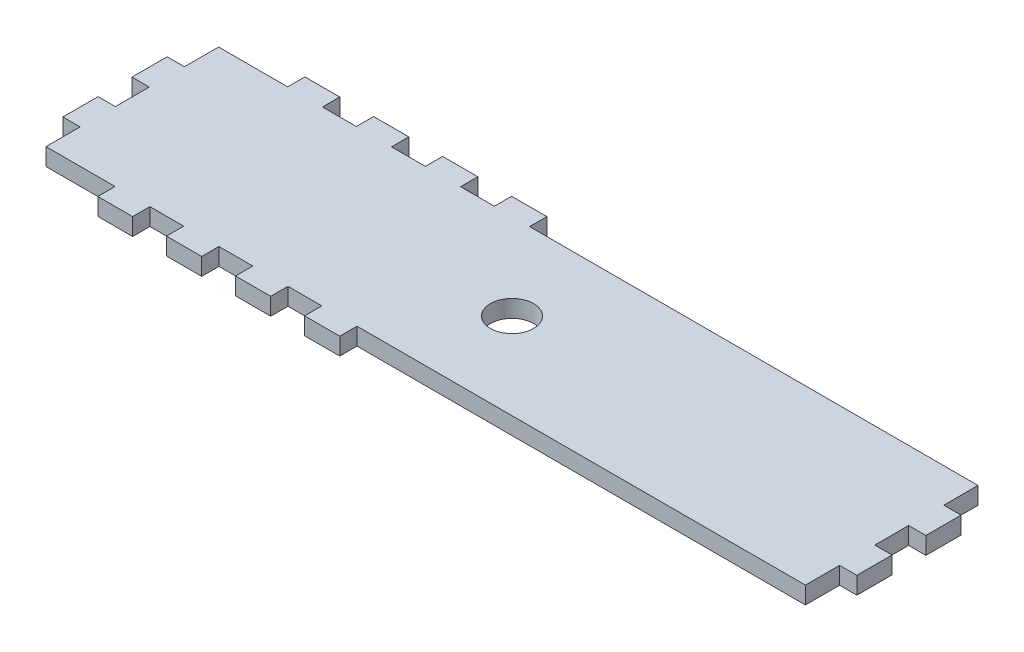
SolidWorks part; units mm, degrees
material "Maple"
ref_plane "Front Plane" through (0, 0, 0) normal (0, 0, 1) x (1, 0, 0)
ref_plane "Top Plane" through (0, 0, 0) normal (0, 1, 0) x (1, 0, 0)
ref_plane "Right Plane" through (0, 0, 0) normal (1, 0, 0) x (0, 0, -1)
sketch "Sketch1" plane through (0, 0, 0) normal (0, 1, 0) x (1, 0, 0)
  line L0 (0, 0) -> (279.4, 0) construction
  line L1 (279.4, 0) -> (279.4, -12.573)
  line L2 (279.4, -12.573) -> (285.75, -12.573)
  line L3 (285.75, -12.573) -> (285.75, -25.527)
  line L4 (285.75, -25.527) -> (279.4, -25.527)
  line L5 (279.4, -25.527) -> (279.4, -37.973)
  line L6 (279.4, -37.973) -> (285.75, -37.973)
  line L7 (285.75, -37.973) -> (285.75, -50.927)
  line L8 (285.75, -50.927) -> (279.4, -50.927)
  line L9 (279.4, -50.927) -> (279.4, -63.5)
  line L10 (279.4, -63.5) -> (0, -63.5) construction
  line L11 (0, -63.5) -> (0, -50.927)
  line L12 (0, -50.927) -> (-6.35, -50.927)
  line L13 (-6.35, -50.927) -> (-6.35, -37.973)
  line L14 (-6.35, -37.973) -> (0, -37.973)
  line L15 (0, -37.973) -> (0, -25.527)
  line L16 (0, -25.527) -> (-6.35, -25.527)
  line L17 (-6.35, -25.527) -> (-6.35, -12.573)
  line L18 (-6.35, -12.573) -> (0, -12.573)
  line L19 (0, -12.573) -> (0, 0)
  line L20 (25.4, 0) -> (25.4, 6.35)
  line L21 (25.4, 6.35) -> (38.227, 6.35)
  line L22 (38.227, 6.35) -> (38.227, 0)
  line L23 (50.673, 0) -> (50.673, 6.35)
  line L24 (50.673, 6.35) -> (63.627, 6.35)
  line L25 (63.627, 6.35) -> (63.627, 0)
  line L26 (76.073, 0) -> (76.073, 6.35)
  line L27 (76.073, 6.35) -> (89.027, 6.35)
  line L28 (89.027, 6.35) -> (89.027, 0)
  line L29 (101.473, 0) -> (101.473, 6.35)
  line L30 (101.473, 6.35) -> (114.427, 6.35)
  line L31 (114.427, 6.35) -> (114.427, 0)
  line L32 (279.4, 0) -> (114.427, 0)
  line L33 (101.473, 0) -> (89.027, 0)
  line L34 (76.073, 0) -> (63.627, 0)
  line L35 (50.673, 0) -> (38.227, 0)
  line L36 (25.4, 0) -> (0, 0)
  line L37 (279.4, -31.75) -> (0, -31.75) construction
  line L38 (0, -63.5) -> (279.4, -63.5) construction
  line L39 (25.4, -63.5) -> (0, -63.5)
  line L40 (50.673, -63.5) -> (38.227, -63.5)
  line L41 (76.073, -63.5) -> (63.627, -63.5)
  line L42 (101.473, -63.5) -> (89.027, -63.5)
  line L43 (279.4, -63.5) -> (114.427, -63.5)
  line L44 (114.427, -69.85) -> (114.427, -63.5)
  line L45 (101.473, -69.85) -> (114.427, -69.85)
  line L46 (101.473, -63.5) -> (101.473, -69.85)
  line L47 (89.027, -69.85) -> (89.027, -63.5)
  line L48 (76.073, -69.85) -> (89.027, -69.85)
  line L49 (76.073, -63.5) -> (76.073, -69.85)
  line L50 (63.627, -69.85) -> (63.627, -63.5)
  line L51 (50.673, -69.85) -> (63.627, -69.85)
  line L52 (50.673, -63.5) -> (50.673, -69.85)
  line L53 (38.227, -69.85) -> (38.227, -63.5)
  line L54 (25.4, -69.85) -> (38.227, -69.85)
  line L55 (25.4, -63.5) -> (25.4, -69.85)
  circle A0 centre (139.7, -31.75) radius 7.9375
  dimension "D17" = 15.875
  dimension "D2" = 6.35
  dimension "D3" = 6.35
  dimension "D4" = 12.954
  dimension "D5" = 12.954
  dimension "D6" = 63.5
  dimension "D7" = 12.573
  dimension "D8" = 12.446
  dimension "D10" = 12.954
  dimension "D11" = 12.446
  dimension "D12" = 12.954
  dimension "D13" = 6.35
  dimension "D14" = 6.35
  dimension "D15" = 279.4
  dimension "D16" = 6.35
  dimension "D18" = 31.75
  dimension "D19" = 139.7
  dimension "D20" = 12.827
  dimension "D21" = 6.35
  dimension "D22" = 12.954
  dimension "D23" = 6.35
  dimension "D24" = 12.446
  dimension "D25" = 25.4
  dimension "D26" = 12.954
  dimension "D27" = 12.954
  dimension "D28" = 6.35
  dimension "D29" = 6.35
  dimension "D30" = 12.446
  dimension "D31" = 12.446
extrude "Boss-Extrude1" add sketch "Sketch1" along normal blind 6.35
